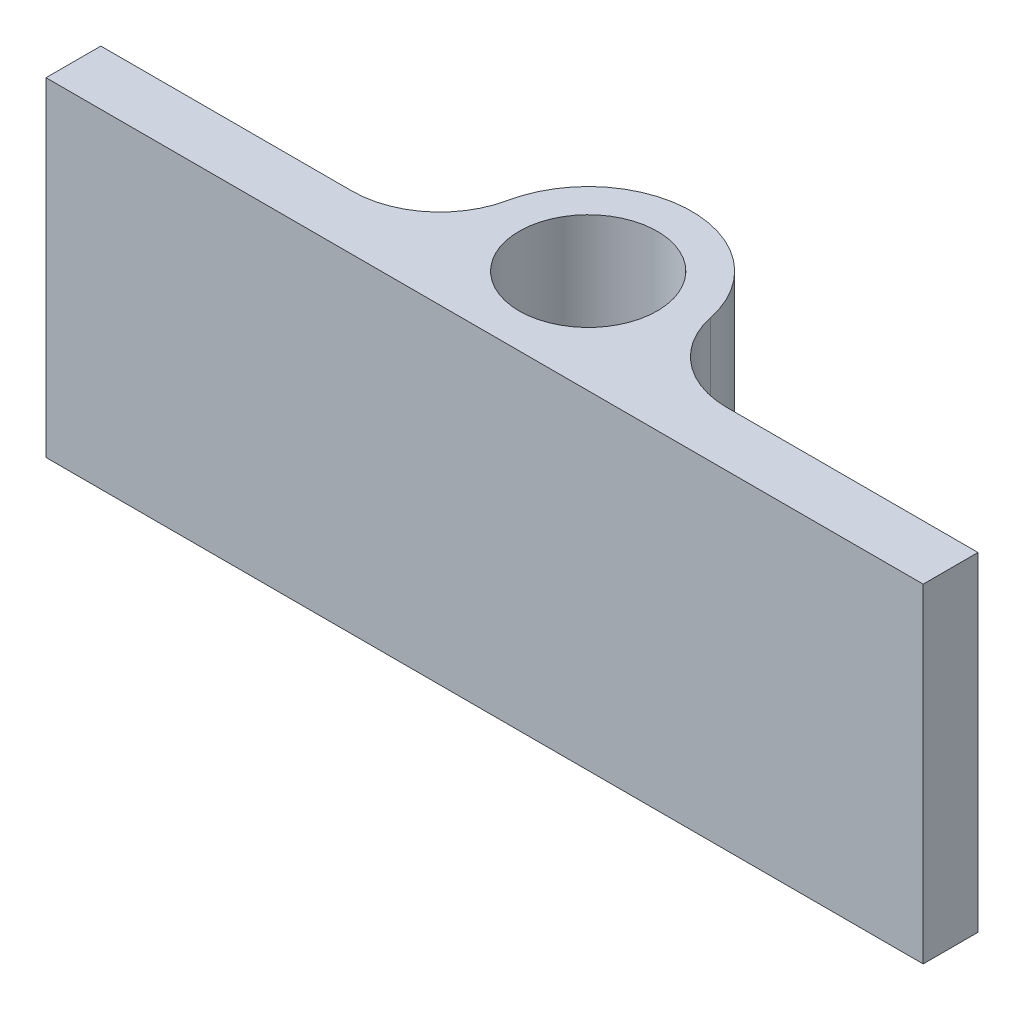
SolidWorks part; units mm, degrees
material "LWPLA"
ref_plane "Front Plane" through (0, 0, 0) normal (0, 0, 1) x (1, 0, 0)
ref_plane "Top Plane" through (0, 0, 0) normal (0, 1, 0) x (1, 0, 0)
ref_plane "Right Plane" through (0, 0, 0) normal (1, 0, 0) x (0, 0, -1)
sketch "Sketch1" plane through (0, 0, 0) normal (0, 1, 0) x (1, 0, 0)
  line L0 (-12.7, -3) -> (12.7, -3)
  line L1 (-12.7, -3) -> (-12.7, -1.4125)
  line L2 (-12.7, -1.4125) -> (-2.6467, -1.4125)
  line L3 (0, -3) -> (0, 3) construction
  line L4 (12.7, -3) -> (12.7, -1.4125)
  line L5 (12.7, -1.4125) -> (2.6467, -1.4125)
  circle A0 centre (0, 0) radius 2
  circle A1 centre (0, 0) radius 3
  point P7 (0, -3)
  dimension "D1" = 4
  dimension "D2" = 6
  dimension "D3" = 25.4
  dimension "D4" = 1.5875
extrude "Boss-Extrude1" add sketch "Sketch1" along normal blind 9.525 contours A1 L2 L1 L0 | A1 L0 L4 L5 | L3 A1 A0 | A1 L3 A0
fillet "Fillet1" radius 2.54 2 edges at (-2.6467, 4.7625, 1.4125) (2.6467, 4.7625, 1.4125)
